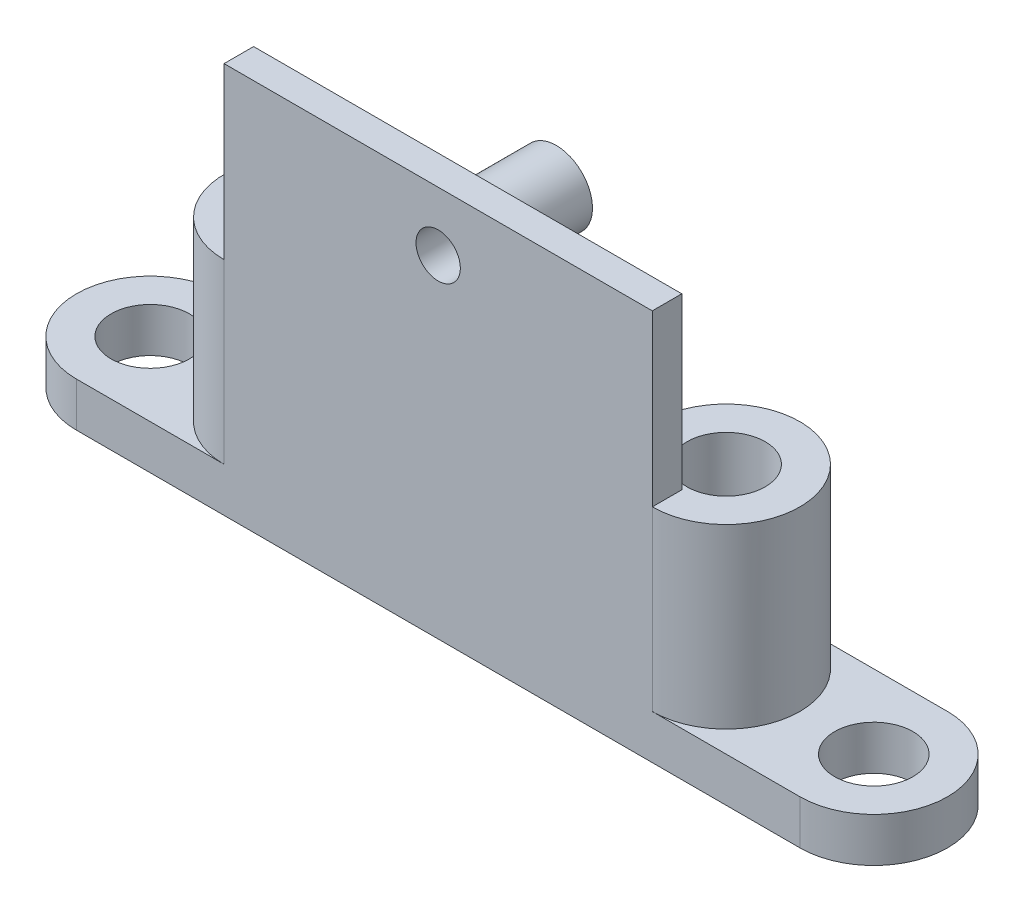
SolidWorks part; units mm, degrees
other "Marquage1"
sketch "Esquisse6" plane through (39, 15, 0) normal (0.0122, 0.9979, 0.0643) x (0.9817, -0.0242, 0.1888)
sketch "Esquisse9" plane through (49.0019, 15, 0) normal (0.0122, 0.9979, 0.0643) x (0.9817, -0.0242, 0.1888)
sketch "Esquisse16" plane through (49.0019, 26.5, 0) normal (0.0122, 0.9979, 0.0643) x (0.9817, -0.0242, 0.1888)
ref_plane "Plan de face" through (0, 0, 0) normal (0, 0, 1) x (1, 0, 0)
ref_plane "Plan de dessus" through (0, 0, 0) normal (0, 1, 0) x (1, 0, 0)
ref_plane "Plan de droite" through (0, 0, 0) normal (1, 0, 0) x (0, 0, -1)
sketch "Esquisse1" plane through (0, 0, 0) normal (0, 1, 0) x (1, 0, 0)
  line L0 (5, 5) -> (34, 5) construction
  line L1 (5, 0) -> (34, 0)
  line L3 (5, 10) -> (34, 10)
  line L5 (0, 10) -> (10, 0) construction
  circle A0 centre (5, 5) radius 2.65
  circle A1 centre (34, 5) radius 2.65
  arc A2 (5, 10) -> (5, 0) centre (5, 5) ccw
  arc A3 (34, 0) -> (34, 10) centre (34, 5) ccw
  point P12 (5, 5)
  dimension "D2" = 5.3
  dimension "D3" = 5.3
  dimension "D1" = 29
extrude "Boss.-Extru.1" add sketch "Esquisse1" along normal blind 15
sketch "Esquisse2" plane through (0, 0, 0) normal (0, -1, 0) x (1, 0, 0)
  circle A0 centre (5, -5) radius 3.4889
  circle A1 centre (34, -5) radius 3.5738
extrude "Boss.-Extru.2" add sketch "Esquisse2" against normal blind 4
sketch "Esquisse3" plane through (0, 15, 0) normal (0, 1, 0) x (1, 0, 0)
  line L0 (5, 10) -> (34, 10)
  line L1 (5, 0) -> (34, 0)
  arc A0 (5, 0) -> (5, 10) centre (5, 5) ccw
  arc A1 (34, 10) -> (34, 0) centre (34, 5) ccw
extrude "Enlèv. mat.-Extru.1" cut sketch "Esquisse3" against normal blind 5
sketch "Esquisse8" plane through (0, 0, 0) normal (0, -1, 0) x (1, 0, 0)
  line L0 (44.0019, -5) -> (-5.0019, -5) construction
  line L1 (44.0019, -10) -> (-5.0019, -10)
  line L2 (44.0019, 0) -> (-5.0019, 0)
  line L3 (5, 0) -> (34, 0) construction
  line L4 (34, -10) -> (5, -10) construction
  arc A0 (44.0019, -10) -> (44.0019, 0) centre (44.0019, -5) ccw
  arc A1 (-5.0019, 0) -> (-5.0019, -10) centre (-5.0019, -5) ccw
  circle A2 centre (-5.0019, -5) radius 2.65
  circle A3 centre (44.0019, -5) radius 2.65
  point P2 (19.5, -5)
  point P13 (19.5, 0)
  dimension "D1" = 5.3
  dimension "D2" = 5.3
extrude "Boss.-Extru.3" add sketch "Esquisse8" against normal blind 3
sketch "Esquisse10" plane through (0, 10, 0) normal (0, 1, 0) x (1, 0, 0)
  line L5 (5, 0) -> (34, 0) construction
  line L10 (29.5, 0) -> (9.5, 0)
  line L11 (29.5, 0) -> (29.5, 1)
  line L12 (29.5, 1) -> (9.5, 1)
  line L13 (9.5, 0) -> (9.5, 1)
  line L14 (34, 10) -> (5, 10) construction
  point P8 (19.5, 10)
  point P9 (19.5, 1)
  dimension "D1" = 20
  dimension "D2" = 1
extrude "Boss.-Extru.4" add sketch "Esquisse10" along normal blind 12.5
sketch "Esquisse11" plane through (0, 0, -1) normal (0, 0, -1) x (-1, 0, 0)
  line L0 (-29.5, 22.5) -> (-9.5, 22.5) construction
  circle A0 centre (-19.5, 22.5) radius 2.45
  circle A1 centre (-19.5, 22.5) radius 1.5
  dimension "D1" = 4.9
  dimension "D2" = 3
extrude "Boss.-Extru.5" add sketch "Esquisse11" along normal blind 7
sketch "Esquisse12" plane through (0, 22.5, 0) normal (0, 1, 0) x (1, 0, 0)
  line L1 (29.5, 1) -> (9.5, 1)
  line L2 (29.5, 1) -> (29.5, 0)
  line L3 (29.5, 0) -> (9.5, 0)
  line L4 (9.5, 1) -> (9.5, 0)
extrude "Boss.-Extru.6" add sketch "Esquisse12" along normal blind 4
sketch "Esquisse13" plane through (0, 0, -1) normal (0, 0, -1) x (-1, 0, 0)
  circle A0 centre (-19.5, 22.5) radius 3.5
  dimension "D1" = 7
extrude "Boss.-Extru.7" add sketch "Esquisse13" along normal blind 1.5
sketch "Esquisse14" plane through (0, 0, -8) normal (0, 0, -1) x (-1, 0, 0)
  circle A0 centre (-19.5, 22.5) radius 1.5
extrude "Enlèv. mat.-Extru.2" cut sketch "Esquisse14" against normal through all
sketch "Esquisse15" plane through (0, 0, 0) normal (0, 0, 1) x (1, 0, 0)
  line L0 (34, 10) -> (34, 3) construction
  line L1 (5, 10) -> (34, 10)
  line L2 (5, 10) -> (5, 26.5)
  line L3 (5, 26.5) -> (34, 26.5)
  line L4 (34, 10) -> (34, 26.5)
  line L5 (9.5, 26.5) -> (29.5, 26.5) construction
  circle A0 centre (19.5, 22.5) radius 1.5
extrude "Boss.-Extru.8" add sketch "Esquisse15" against normal blind 2
fillet "Congé1" radius 2 1 edges at (19.5, 10, -2)
